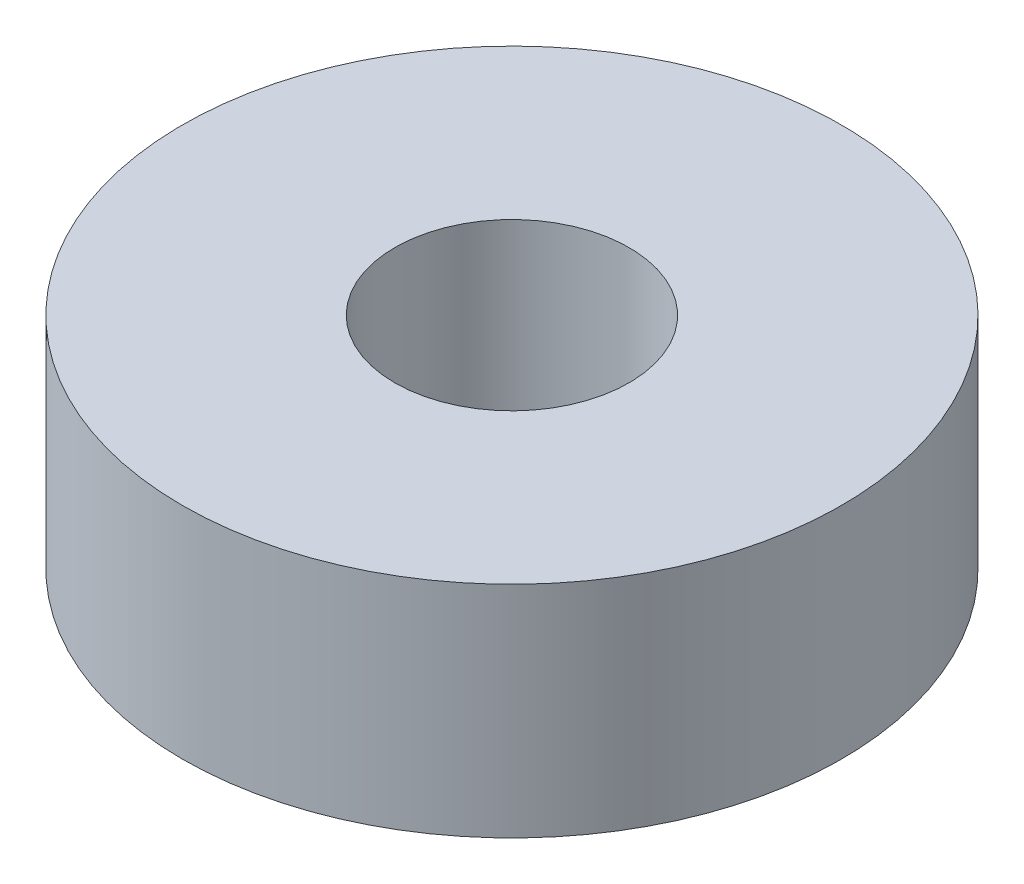
SolidWorks part; units mm, degrees
ref_plane "前视基准面" through (0, 0, 0) normal (0, 0, 1) x (1, 0, 0)
ref_plane "上视基准面" through (0, 0, 0) normal (0, 1, 0) x (1, 0, 0)
ref_plane "右视基准面" through (0, 0, 0) normal (1, 0, 0) x (0, 0, -1)
sketch "草图1" plane through (0, 0, 0) normal (0, 1, 0) x (1, 0, 0)
  circle A0 centre (0, 0) radius 22.5
  circle A1 centre (0, 0) radius 8
  dimension "D1" = 45
  dimension "D2" = 16
extrude "凸台-拉伸1" add sketch "草图1" along normal blind 15
